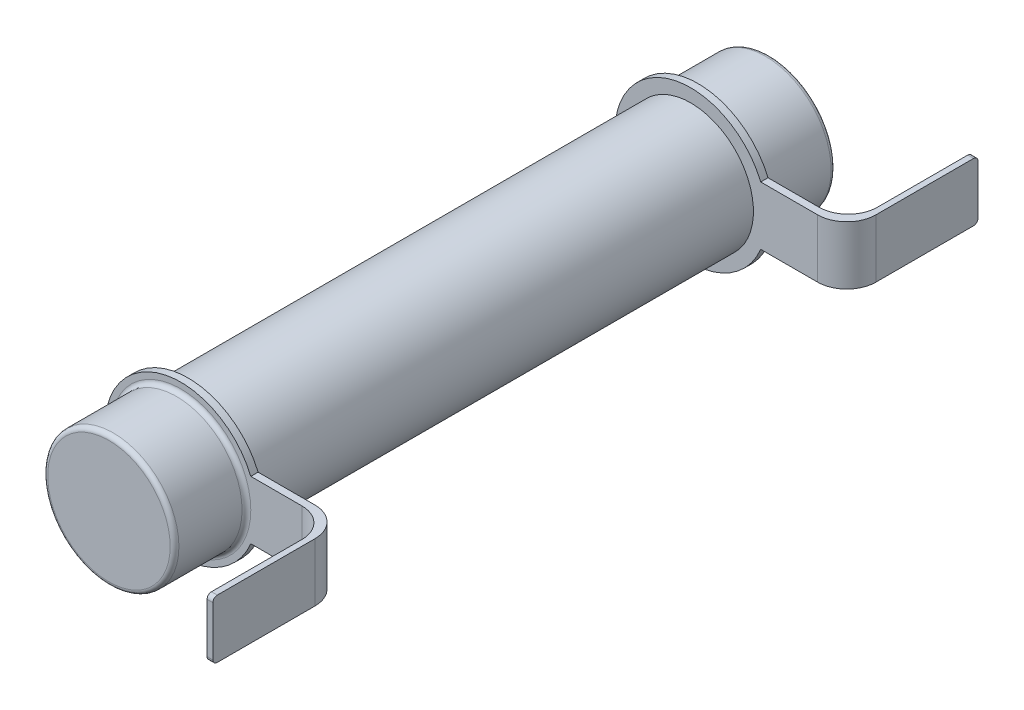
SolidWorks part; units mm, degrees
ref_plane "Front Plane" through (0, 0, 0) normal (0, 0, 1) x (1, 0, 0)
ref_plane "Top Plane" through (0, 0, 0) normal (0, 1, 0) x (1, 0, 0)
ref_plane "Right Plane" through (0, 0, 0) normal (1, 0, 0) x (0, 0, -1)
sketch "Sketch1" plane through (0, 0, 0) normal (0, 0, 1) x (1, 0, 0)
  circle A0 centre (0, 0) radius 4.3
  dimension "D1" = 8.6
extrude "Boss-Extrude1" add sketch "Sketch1" along normal mid plane 45.33
sketch "Sketch2" plane through (0, 0, 22.665) normal (0, 0, 1) x (1, 0, 0)
  circle A0 centre (0, 0) radius 4.5
  circle A1 centre (0, 0) radius 4.3 construction
  circle A2 centre (0, 0) radius 4.3
  dimension "D1" = 9
extrude "Boss-Extrude2" add sketch "Sketch2" against normal blind 5.43
ref_plane "Plane1" through (0, 0, 17.235) normal (0, 0, 1) x (1, 0, 0)
sketch "Sketch3" plane through (0, 0, 17.235) normal (0, 0, 1) x (1, 0, 0)
  circle A0 centre (0, 0) radius 5.2
  circle A1 centre (0, 0) radius 4.5 construction
  circle A2 centre (0, 0) radius 4.5
  dimension "D1" = 10.4
extrude "Boss-Extrude3" add sketch "Sketch3" along normal blind 0.5
mirror "Mirror1" about plane through (0, 0, 0) normal (0, 0, 1) of "Boss-Extrude2", "Boss-Extrude3"
ref_plane "Plane2" through (10.7, 0, 0) normal (1, 0, 0) x (0, 0, -1)
sketch "Sketch5" plane through (10.7, 0, 0) normal (1, 0, 0) x (0, 0, -1)
  line L0 (17.235, 5.2) -> (17.235, -5.2) construction
  line L1 (17.235, 2) -> (26.235, 2)
  line L2 (17.235, 2) -> (17.235, -2)
  line L3 (17.235, -2) -> (26.235, -2)
  line L4 (26.235, 2) -> (26.235, -2)
  line L5 (17.235, 2) -> (26.235, -2) construction
  line L6 (17.235, -2) -> (26.235, 2) construction
  point P0 (21.735, 0)
  point P7 (0, 0)
  dimension "D1" = 4
  dimension "D2" = 9
extrude "Boss-Extrude4" add sketch "Sketch5" against normal blind 0.4 separate body
sketch "Sketch6" plane through (10.3, 0, 0) normal (-1, 0, 0) x (0, 0, 1)
  line L0 (-17.735, 4.5) -> (-17.735, -4.5) construction
  line L1 (-17.735, 2) -> (-17.235, 2)
  line L2 (-17.735, 2) -> (-17.735, -2)
  line L3 (-17.735, -2) -> (-17.235, -2)
  line L4 (-17.235, 2) -> (-17.235, -2)
  line L5 (-17.235, -5.2) -> (-17.235, 5.2) construction
  line L6 (-17.235, -2) -> (-26.235, -2) construction
  line L7 (-26.235, 2) -> (-17.235, 2) construction
  point P10 (0, 0)
extrude "Boss-Extrude5" add sketch "Sketch6" along normal up to surface (5.5 mm away)
sketch "Sketch7" plane through (10.7, 0, 0) normal (1, 0, 0) x (0, 0, -1)
  line L0 (-17.235, 4.62) -> (-17.235, -4.62) construction
  line L1 (-26.235, 2) -> (-17.235, 2)
  line L2 (-26.235, 2) -> (-26.235, -2)
  line L3 (-26.235, -2) -> (-17.235, -2)
  line L4 (-17.235, 2) -> (-17.235, -2)
  line L5 (-26.235, 2) -> (-17.235, -2) construction
  line L6 (-26.235, -2) -> (-17.235, 2) construction
  point P0 (-21.735, 0)
  point P7 (0, 0)
  dimension "D1" = 4
  dimension "D2" = 9
extrude "Boss-Extrude6" add sketch "Sketch7" against normal blind 0.4 separate body
sketch "Sketch8" plane through (10.3, 0, 0) normal (-1, 0, 0) x (0, 0, 1)
  line L0 (17.235, -4.62) -> (17.235, 4.62) construction
  line L1 (17.235, 2) -> (17.735, 2)
  line L2 (17.235, 2) -> (17.235, -2)
  line L3 (17.235, -2) -> (17.735, -2)
  line L4 (17.735, 2) -> (17.735, -2)
  line L5 (17.735, -4.5) -> (17.735, 4.5) construction
  line L6 (26.235, -2) -> (17.235, -2) construction
  line L7 (17.235, 2) -> (26.235, 2) construction
extrude "Boss-Extrude7" add sketch "Sketch8" along normal up to surface (5.5 mm away)
fillet "Fillet2" radius 2 4 edges at (10.7, 0, 17.235) (10.3, 0, 17.735) (10.7, 0, -17.235) (10.3, 0, -17.735)
fillet "Fillet3" radius 0.3 7 edges at (4.5, 0, -22.665) (4.5, 0, 17.735) (4.5, 0, 22.665) (10.5, 2, 26.235) (10.5, -2, 26.235) (10.5, 2, -26.235) (10.5, -2, -26.235)
